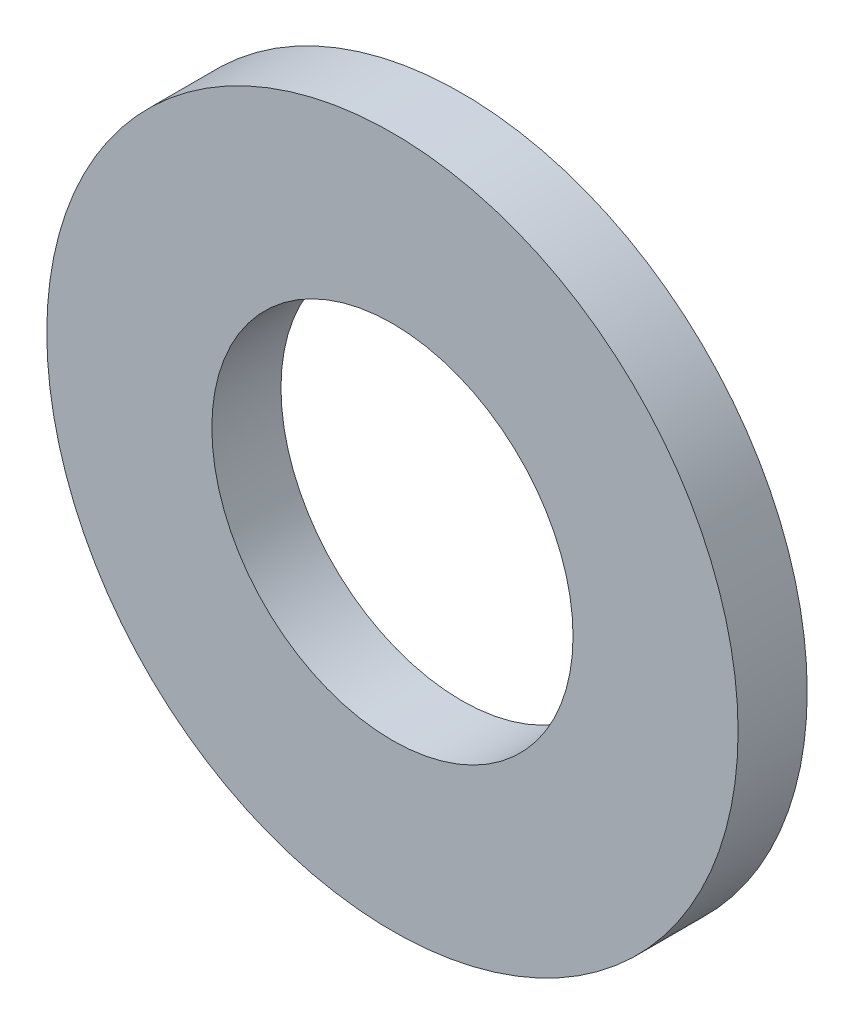
SolidWorks part; units mm, degrees
ref_plane "Front" through (0, 0, 0) normal (0, 0, 1) x (1, 0, 0)
ref_plane "Top" through (0, 0, 0) normal (0, 1, 0) x (1, 0, 0)
ref_plane "Right" through (0, 0, 0) normal (1, 0, 0) x (0, 0, -1)
sketch "Sketch1" plane through (0, 0, 0) normal (0, 0, 1) x (1, 0, 0)
  circle A0 centre (0, 0) radius 2.09
  circle A1 centre (0, 0) radius 4
  dimension "d1" = 4.18
  dimension "d2" = 8
extrude "Base-Extrude" add sketch "Sketch1" against normal blind 0.8
